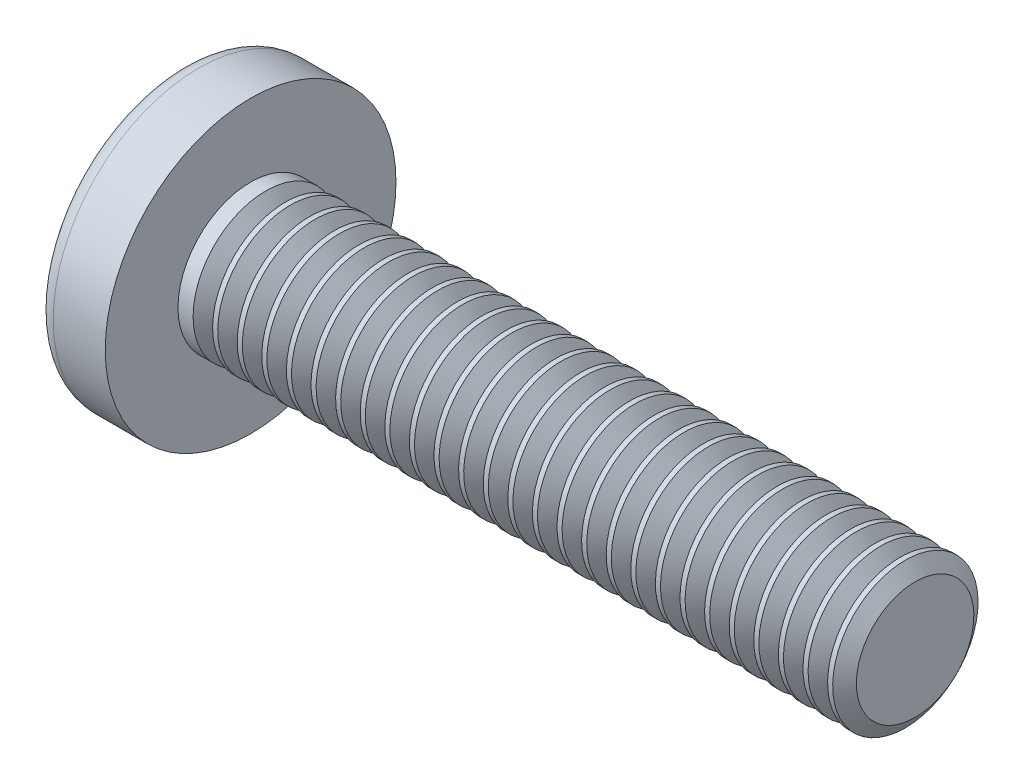
SolidWorks part; units mm, degrees
ref_plane "Plane1" through (0, 0, 0) normal (0, 0, 1) x (1, 0, 0)
ref_plane "Plane2" through (0, 0, 0) normal (0, 1, 0) x (1, 0, 0)
ref_plane "Plane3" through (0, 0, 0) normal (1, 0, 0) x (0, 0, -1)
sketch "BodySke" plane through (0, 0, 0) normal (0, 0, 1) x (1, 0, 0)
  line L0 (2.6, 1.75) -> (2.6, 3.5)
  line L1 (3.2, 6.35) -> (3.2, -3.175) construction
  line L2 (-25.4, 0) -> (127, 0) construction
  line L3 (18.6, 0) -> (0, 0)
  line L4 (2.6, 1.75) -> (18.6, 1.75)
  line L5 (18.6, 1.75) -> (18.6, 0)
  line L6 (1.347, 3.5) -> (2.6, 3.5)
  line L7 (2.6, -1.75) -> (18.6, -1.75) construction
  line L8 (2.6, 6.35) -> (2.6, -3.175) construction
  arc A0 (0.9968, 3.3118) -> (0, 0) centre (6, 0) ccw
  arc A2 (0.9968, 3.3118) -> (1.347, 3.5) centre (1.347, 3.08) cw
  dimension "Head_crown_rad" = 6
  dimension "Head_fillet_rad" = 0.42
  dimension "Diameter" = 3.5
  dimension "Head_ht" = 2.6
  dimension "Head_dia" = 7
  dimension "Advance" = 0.6
revolve "Base-Revolve" add sketch "BodySke" angle 360 about L2
cosmetic thread "ThreadCosmetic" [suppressed] parameters "Thread_length"=15.4, "Thread_minor"=2.829
sketch "Sketch3" plane through (0, 0, 0) normal (1, 0, 0) x (0, 0, -1)
  line L0 (0.435, -1.96) -> (-0.435, -1.96)
  line L1 (0.435, -1.96) -> (0.435, 1.96)
  line L2 (-0.435, 1.96) -> (0.435, 1.96)
  line L3 (-0.435, 1.96) -> (-0.435, -1.96)
  dimension "Cross_dia" = 3.92
  dimension "D1" = 1.96
  dimension "Cross_width" = 0.87
  dimension "D2" = 0.435
ref_plane "Plane4" through (1.95, 0, 0) normal (1, 0, 0) x (0, 0, -1)
sketch "Sketch4" plane through (1.95, 0, 0) normal (1, 0, 0) x (0, 0, -1)
  line L0 (0.2175, -0.2175) -> (-0.2175, -0.2175)
  line L1 (0.2175, -0.2175) -> (0.2175, 0.2175)
  line L2 (-0.2175, 0.2175) -> (0.2175, 0.2175)
  line L3 (-0.2175, 0.2175) -> (-0.2175, -0.2175)
  dimension "D2" = 0.435
  dimension "D1" = 0.435
  dimension "D3" = 0.2175
  dimension "D4" = 0.2175
loft "Cut-Loft1" cut profiles "Sketch3", "Sketch4"
pattern_circular "CirPattern1" count 2 every 90 about axis through (0, 0, 0) along (1, 0, 0) of "Cut-Loft1"
sketch "ThdSchSke" plane through (0, 0, 0) normal (0, 0, 1) x (1, 0, 0)
  line L0 (3.2, -1.4145) -> (2.9651, -1.75)
  line L1 (3.2, -1.4145) -> (3.4349, -1.75)
  line L2 (3.4349, -1.75) -> (3.4349, -2.1875)
  line L3 (-3.175, 0) -> (5.1513, 0) construction
  line L5 (3.4349, -2.1875) -> (2.9651, -2.1875)
  line L6 (2.9651, -2.1875) -> (2.9651, -1.75)
  dimension "Diameter" = 3.5
  dimension "SideAngle" = 55
  dimension "VeeAngle" = 70
  dimension "Thread_minor" = 2.829
  dimension "Overcut" = 4.375
  dimension "Start" = 3.2
revolve "ThreadSchematic" cut sketch "ThdSchSke" angle 360 about L3
pattern_linear "ThdSchPat" count 27 spacing 0.5923 along (1, 0, 0) of "ThreadSchematic"
equation "\"D1@Sketch3\" = \"Cross_dia@Sketch3\" / 2"
equation "\"D2@Sketch3\" = \"Cross_width@Sketch3\" / 2"
equation "\"D1@Sketch4\" = \"Cross_width@Sketch3\" *.5"
equation "\"D2@Sketch4\" = \"D1@Sketch4\""
equation "\"D3@Sketch4\" = \"D1@Sketch4\" / 2"
equation "\"D4@Sketch4\" = \"D2@Sketch4\" / 2"
equation "\"Thread_length@ThreadCosmetic\" = ((sgn( (\"Length@BodySke\" - \"Advance@BodySke\" ) - \"Thread_nom@BodySke\" )-1)*( (\"Length@BodySke\" - \"Advance@BodySke\" ) - \"Thread_nom@BodySke\" ))/-2+ \"Thread_nom@BodySke\""
equation "\"Thread_minor@ThdSchSke\" = \"Thread_minor@ThreadCosmetic\""
equation "\"Diameter@ThdSchSke\" = \"Diameter@BodySke\""
equation "\"Overcut@ThdSchSke\" = \"Diameter@BodySke\" * 1.25"
equation "\"Start@ThdSchSke\" = \"Head_ht@BodySke\" + \"Length@BodySke\" - \"Thread_length@ThreadCosmetic\"  '---Non-countersunk---"
equation "\"Num_threads@ThdSchPat\" = int( \"Thread_length@ThreadCosmetic\" / \"Advance@BodySke\" + 0.999 )  + 1"
equation "\"Advance@ThdSchPat\" = \"Thread_length@ThreadCosmetic\" /  (\"Num_threads@ThdSchPat\" - 1) 'relax it"
